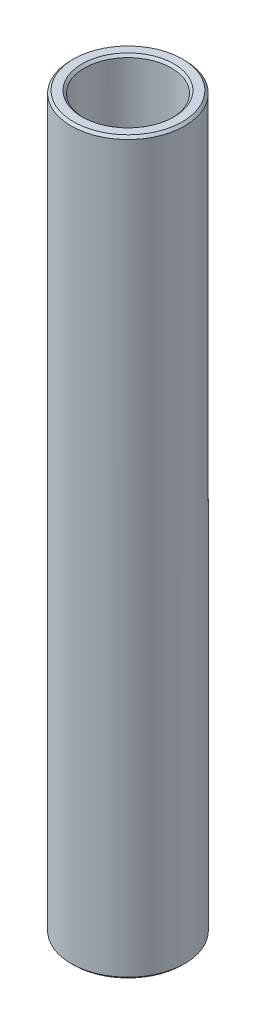
SolidWorks part; units mm, degrees
ref_plane "Front Plane" through (0, 0, 0) normal (0, 0, 1) x (1, 0, 0)
ref_plane "Top Plane" through (0, 0, 0) normal (0, 1, 0) x (1, 0, 0)
ref_plane "Right Plane" through (0, 0, 0) normal (1, 0, 0) x (0, 0, -1)
sketch "Sketch1" plane through (0, 0, 0) normal (0, 0, 1) x (1, 0, 0)
  line L0 (0, 12.832) -> (0, -12.832) construction
  line L1 (2.3, 19.275) -> (2.3, -19.275)
  line L2 (2.3, -19.275) -> (3, -19.275)
  line L3 (3, -19.275) -> (3, 19.275)
  line L4 (3, 19.275) -> (2.3, 19.275)
  point P5 (2.3, 0)
  dimension "D1" = 38.55
  dimension "D2" = 6
  dimension "D3" = 4.6
revolve "Revolve1" add sketch "Sketch1" angle 360 about L0
chamfer "Chamfer1" distance 0.127 angle 45 4 edges at (0, -19.275, 2.3) (0, -19.275, 3) (0, 19.275, 3) (0, 19.275, 2.3)
